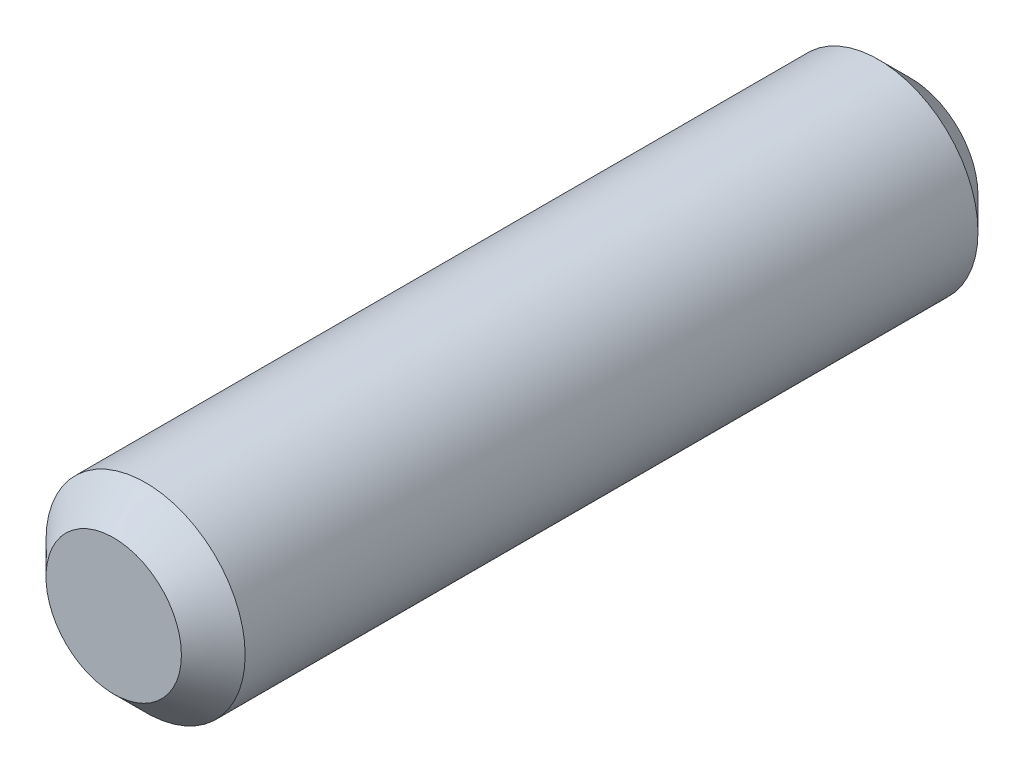
SolidWorks part; units mm, degrees
material "6061-T6 (SS)"
ref_plane "Front Plane" through (0, 0, 0) normal (0, 0, 1) x (1, 0, 0)
ref_plane "Top Plane" through (0, 0, 0) normal (0, 1, 0) x (1, 0, 0)
ref_plane "Right Plane" through (0, 0, 0) normal (1, 0, 0) x (0, 0, -1)
sketch "Sketch1" plane through (0, 0, 0) normal (0, 0, 1) x (1, 0, 0)
  circle A0 centre (0, 0) radius 1.5875
  dimension "D1" = 3.175
extrude "Boss-Extrude1" add sketch "Sketch1" along normal blind 12.7
chamfer "Chamfer1" distance 0.508 angle 45 2 edges at (1.5875, 0, 0) (1.5875, 0, 12.7)
